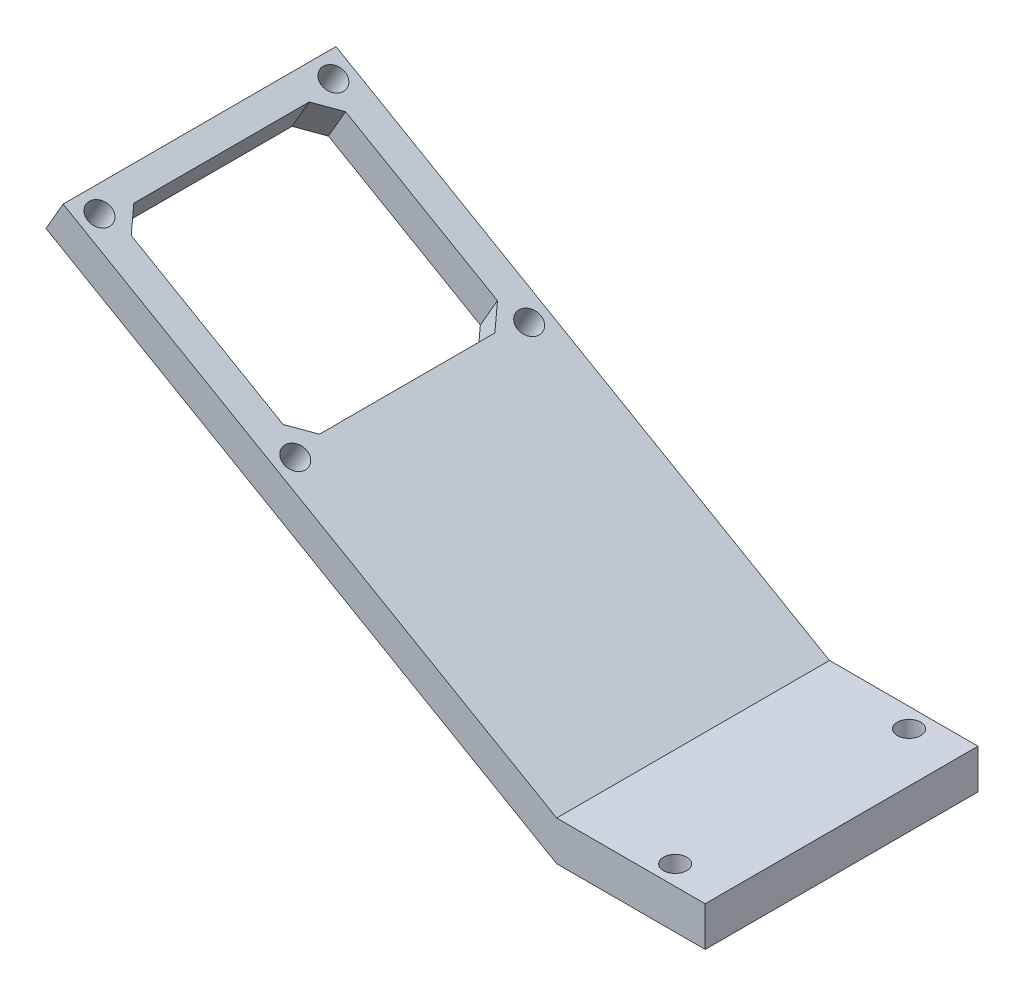
SolidWorks part; units mm, degrees
ref_plane "Front Plane" through (0, 0, 0) normal (0, 0, 1) x (1, 0, 0)
ref_plane "Top Plane" through (0, 0, 0) normal (0, 1, 0) x (1, 0, 0)
ref_plane "Right Plane" through (0, 0, 0) normal (1, 0, 0) x (0, 0, -1)
sketch "Sketch2" plane through (0, 0, 0) normal (0, 0, 1) x (1, 0, 0)
  line L0 (-35.1953, 15.24) -> (0, -5.08)
  line L1 (19.05, -5.08) -> (0, -5.08)
  line L2 (19.05, -5.08) -> (19.05, 0)
  line L3 (19.05, 0) -> (0, 0)
  line L4 (0, -5.08) -> (0, 0)
  line L5 (-35.1953, 15.24) -> (-32.9956, 19.05)
  line L6 (-32.9956, 19.05) -> (0, 0)
  line L7 (-35.1953, 15.24) -> (-32.9956, 19.05)
  line L8 (-35.1953, 15.24) -> (-65.5062, 32.74)
  line L9 (-32.9956, 19.05) -> (-63.3065, 36.55)
  line L10 (-65.5062, 32.74) -> (-63.3065, 36.55)
  dimension "D2" = 5.08
  dimension "D3" = 19.05
  dimension "D4" = 38.1
  dimension "D5" = 35
  dimension "30" = 30
extrude "Boss-Extrude1" add sketch "Sketch2" along normal blind 35 contours L10 L8 L5 L9 | L6 L5 L0 L4 | L4 L1 L2 L3
sketch "Sketch3" plane through (0, 0, 0) normal (0.5, 0.866, 0) x (0.866, -0.5, 0)
  line L0 (0, 0) -> (-73.1, 0) construction
  line L1 (-70.6, -2.5) -> (-41.6, -2.5) construction
  line L2 (-70.6, -2.5) -> (-70.6, -32.5) construction
  line L3 (-70.6, -32.5) -> (-41.6, -32.5) construction
  line L4 (-41.6, -2.5) -> (-41.6, -32.5) construction
  line L5 (-73.1, -35) -> (-73.1, 0) construction
  line L6 (-68.6, -17.5) -> (-43.6, -17.5) construction
  line L7 (-68.6, -5) -> (-43.6, -5)
  line L8 (-68.6, -5) -> (-68.6, -30)
  line L9 (-68.6, -30) -> (-43.6, -30)
  line L10 (-43.6, -5) -> (-43.6, -30)
  line L11 (-68.6, -5) -> (-43.6, -5)
  line L12 (-68.6, -5) -> (-68.6, -3.75)
  line L13 (-68.6, -3.75) -> (-43.6, -3.75)
  line L14 (-43.6, -5) -> (-43.6, -3.75)
  line L15 (-43.6, -30) -> (-43.6, -31.25)
  line L16 (-68.6, -31.25) -> (-43.6, -31.25)
  line L17 (-68.6, -30) -> (-68.6, -31.25)
  line L18 (-56.1, -5) -> (-56.1, -30) construction
  line L19 (-68.6, -5) -> (-69.85, -5)
  line L20 (-68.6, -5) -> (-68.6, -30)
  line L21 (-68.6, -30) -> (-69.85, -30)
  line L22 (-69.85, -5) -> (-69.85, -30)
  line L23 (-43.6, -5) -> (-42.35, -5)
  line L24 (-43.6, -30) -> (-42.35, -30)
  line L25 (-42.35, -5) -> (-42.35, -30)
  line L26 (-44.85, -3.75) -> (-42.35, -6.25)
  line L27 (-44.85, -31.25) -> (-42.35, -28.75)
  line L28 (-67.35, -3.75) -> (-69.85, -6.25)
  line L29 (-67.35, -31.25) -> (-69.85, -28.75)
  point P16 (-56.1, -3.75)
  point P17 (-56.1, -5)
  point P30 (-70.6, -17.5)
  point P32 (-56.1, -2.5)
  dimension "D1" = 2.5
  dimension "D2" = 29
  dimension "D3" = 2.5
  dimension "D4" = 30
  dimension "D6" = 25
  dimension "D7" = 1.25
  dimension "D8" = 25
  dimension "D9" = 1.25
extrude "Cut-Extrude1" cut sketch "Sketch3" against normal through all contours L10 L7 L8 L9 | L13 L28 L7 L26 | L29 L8 L28 L22 | L10 L27 L25 L26 | L29 L16 L27 L9
hole_wizard "Ø3.0mm Dowel Hole1" positions "3DSketch1" profile "Sketch4" hole size "Ø3.0" standard "ANSI Metric" end condition through all
sketch3d "3DSketch1"
  point P0 (-61.1414, 35.3, 2.5)
  point P3 (-36.0267, 20.8, 2.5)
  point P6 (-36.0267, 20.8, 32.5)
  point P9 (-61.1414, 35.3, 32.5)
sketch "Sketch4" plane through (-61.1414, 35.3, 2.5) normal (0, 0, 1) x (-0.866, 0.5, 0)
  line L0 (0, 0) -> (0, 37.1525)
  line L1 (0, 37.1525) -> (1.5, 37.1525)
  line L2 (1.5, 37.1525) -> (1.5, 0)
  line L5 (1.5, 0) -> (0, 0)
  line L11 (0, -6.35) -> (0, 107.95) construction
  dimension "Thru Hole Dia." = 3
  dimension "Thru Hole Depth" = 37.1525
sketch "Sketch5" plane through (0, 0, 0) normal (0, 1, 0) x (1, 0, 0)
  line L0 (19.05, -35) -> (19.05, 0) construction
  line L1 (19.05, -2.5) -> (12.7, -2.5)
  line L2 (19.05, -2.5) -> (19.05, -32.5)
  line L3 (19.05, -32.5) -> (12.7, -32.5)
  line L4 (12.7, -2.5) -> (12.7, -32.5)
  point P6 (19.05, -17.5)
  dimension "D1" = 6.35
  dimension "D2" = 30
  dimension "D3" = 17.5
hole_wizard "Ø3.0mm Dowel Hole2" positions "3DSketch2" profile "Sketch6" hole size "Ø3.0" standard "ANSI Metric" end condition through all
sketch3d "3DSketch2"
  point P0 (12.7, 0, 2.5)
  point P3 (12.7, 0, 32.5)
sketch "Sketch6" plane through (12.7, 0, 2.5) normal (1, 0, 0) x (0, 0, 1)
  line L0 (0, 0) -> (0, 5.08)
  line L1 (0, 5.08) -> (1.5, 5.08)
  line L2 (1.5, 5.08) -> (1.5, 0)
  line L5 (1.5, 0) -> (0, 0)
  line L11 (0, -6.35) -> (0, 107.95) construction
  dimension "Thru Hole Dia." = 3
  dimension "Thru Hole Depth" = 5.08
